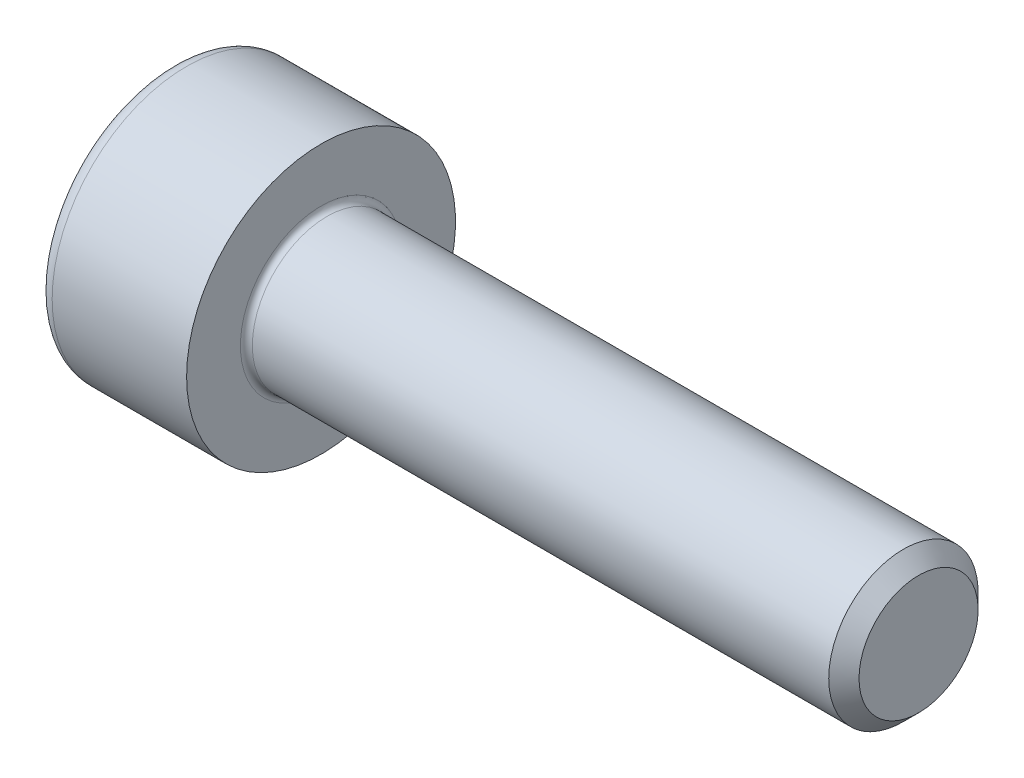
SolidWorks part; units mm, degrees
ref_plane "Plane1" through (0, 0, 0) normal (0, 0, 1) x (1, 0, 0)
ref_plane "Plane2" through (0, 0, 0) normal (0, 1, 0) x (1, 0, 0)
ref_plane "Plane3" through (0, 0, 0) normal (1, 0, 0) x (0, 0, -1)
sketch "BodySke" plane through (0, 0, 0) normal (0, 0, 1) x (1, 0, 0)
  line L0 (0, 0) -> (0, 2.25)
  line L1 (0, 2.25) -> (2.5, 2.25)
  line L2 (2.5, 2.25) -> (2.5, 1.25)
  line L3 (2.5, 1.25) -> (12.2465, 1.25)
  line L4 (12.5, 0.9965) -> (12.5, 0)
  line L5 (12.5, 0) -> (0, 0)
  line L6 (-31.75, 0) -> (127, 0) construction
  line L8 (12.5, 0.9965) -> (12.2465, 1.25)
  line L10 (12.5, -0.9965) -> (12.2465, -1.25) construction
  line L11 (2.95, 9.525) -> (2.95, 3.175) construction
  line L12 (2.5, 9.525) -> (2.5, 3.175) construction
  line L13 (-47.5, 9.525) -> (-47.5, 3.175) construction
  dimension "Diameter" = 2.5
  dimension "Head_ht" = 2.5
  dimension "Length" = 10
  dimension "Body_ch_ang" = 45
  dimension "Head_dia" = 4.5
  dimension "Minor_dia" = 1.993
  dimension "Advance" = 0.45
  dimension "Thread_nom" = 10
  dimension "Thread_length" = 60
revolve "Base-Revolve" add sketch "BodySke"
cosmetic thread "ThreadCosmetic" [suppressed]
fillet "Fillet1" radius 0.1 1 edges at (2.5, 0, 1.25)
fillet "Fillet2" radius 0.25 1 edges at (0, 0, 2.25)
sketch "Sketch2" plane through (0, 0, 0) normal (0, 0, 1) x (1, 0, 0)
  line L0 (0, 1.01) -> (1.1, 1.01)
  line L1 (1.1, 1.01) -> (1.6831, 0)
  line L2 (-31.75, 0) -> (127, 0) construction
  line L3 (1.6831, 0) -> (0, 0)
  line L4 (0, 0) -> (0, 1.01)
  line L6 (0, 0) -> (47.625, 0) construction
  dimension "D1" = 1.01
  dimension "D2" = 60
  dimension "Depth" = 1.1
revolve "Hex-PreBroach" cut sketch "Sketch2" angle 360 about L6
sketch "Sketch3" plane through (0, 0, 0) normal (-1, 0, 0) x (0, 0.5, 0.866)
  line L0 (0.5831, 1.01) -> (-0.5831, 1.01)
  line L1 (-0.5831, 1.01) -> (-1.1662, 0)
  line L2 (0.5831, 1.01) -> (1.1662, 0)
  line L3 (0.5831, -1.01) -> (1.1662, 0)
  line L4 (0.5831, -1.01) -> (-0.5831, -1.01)
  line L5 (-0.5831, -1.01) -> (-1.1662, 0)
  dimension "D1" = 1.01
  dimension "D2" = 1.01
  dimension "Hex_size" = 2.02
extrude "Hex" cut sketch "Sketch3" against normal blind 1.1
sketch "ThdSchSke" plane through (0, 0, 0) normal (0, 0, 1) x (1, 0, 0)
  line L0 (3.85, -0.9965) -> (3.6725, -1.25)
  line L1 (3.85, -0.9965) -> (4.0275, -1.25)
  line L2 (4.0275, -1.25) -> (4.0275, -1.5625)
  line L3 (-3.175, 0) -> (5.1513, 0) construction
  line L4 (0, 2) -> (0, -2) construction
  line L5 (4.0275, -1.5625) -> (3.6725, -1.5625)
  line L6 (3.6725, -1.5625) -> (3.6725, -1.25)
  dimension "Thread_minor" = 1.993
  dimension "Diameter" = 2.5
  dimension "Start" = 3.85
  dimension "SideAngle" = 55
  dimension "VeeAngle" = 70
  dimension "Overcut" = 3.125
revolve "ThreadSchematic" [suppressed] cut sketch "ThdSchSke" angle 360 about L3
pattern_linear "ThdSchPat" [suppressed]
equation "\"D2@Sketch3\" = \"Hex_size@Sketch3\" / 2"
equation "\"D1@Sketch3\" = \"Hex_size@Sketch3\" / 2"
equation "\"D1@Sketch2\" = \"Hex_size@Sketch3\" / 2"
equation "\"Thread_minor@ThreadCosmetic\"  =  \"Minor_dia@BodySke\""
equation "\"Depth@Sketch2\" =  \"Key_eng@Hex\""
equation "\"Thread_length@ThreadCosmetic\" = ((sgn( (\"Length@BodySke\" - \"Advance@BodySke\" * 3.0) - \"Thread_nom@BodySke\" )-1)*( (\"Length@BodySke\" - \"Advance@BodySke\" * 3.0) - \"Thread_nom@BodySke\" ))/-2+ \"Thread_nom@BodySke\""
equation "\"Thread_minor@ThdSchSke\" = \"Minor_dia@BodySke\""
equation "\"Diameter@ThdSchSke\" = \"Diameter@BodySke\""
equation "\"Overcut@ThdSchSke\" = \"Diameter@BodySke\" * 1.25"
equation "\"Start@ThdSchSke\" = \"Head_ht@BodySke\" + \"Length@BodySke\" - \"Thread_length@ThreadCosmetic\"  '---Non-countersunk---"
equation "\"Num_threads@ThdSchPat\" = int( \"Thread_length@ThreadCosmetic\" / \"Advance@BodySke\" + 0.999 )  + 1"
equation "\"Advance@ThdSchPat\" = \"Thread_length@ThreadCosmetic\" /  (\"Num_threads@ThdSchPat\" - 1) 'relax it"
equation "\"Num_threads@ThdSchPat\" = \"Num_threads@ThdSchPat\" - sgn( \"Num_threads@ThdSchPat\" - 1) '---chamfered tips only---"
